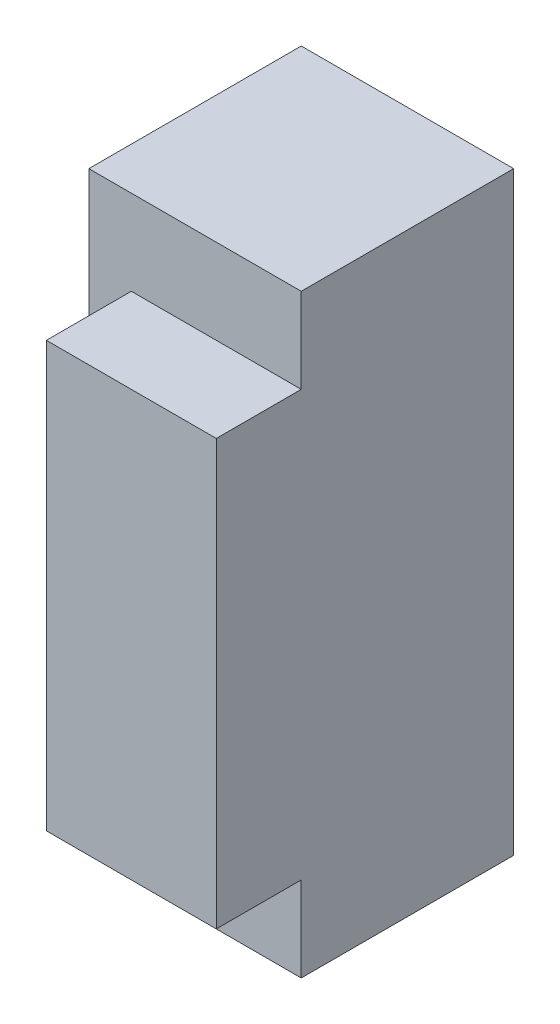
SolidWorks part; units mm, degrees
ref_plane "Front Plane" through (0, 0, 0) normal (0, 0, 1) x (1, 0, 0)
ref_plane "Top Plane" through (0, 0, 0) normal (0, 1, 0) x (1, 0, 0)
ref_plane "Right Plane" through (0, 0, 0) normal (1, 0, 0) x (0, 0, -1)
sketch "Sketch1" plane through (0, 0, 0) normal (0, 0, 1) x (1, 0, 0)
  line L1 (-2.5, 7) -> (2.5, 7)
  line L2 (-2.5, 7) -> (-2.5, -7)
  line L3 (-2.5, -7) -> (2.5, -7)
  line L4 (2.5, 7) -> (2.5, -7)
  point P4 (2.5, 0)
  point P6 (0, 7)
  dimension "D1" = 14
  dimension "D2" = 5
extrude "Extrude1" add sketch "Sketch1" along normal blind 5
sketch "Sketch2" plane through (0, 0, 5) normal (0, 0, 1) x (1, 0, 0)
  line L0 (2.5, -7) -> (2.5, 7) construction
  line L1 (2.5, -5) -> (-1.5, -5)
  line L2 (2.5, -5) -> (2.5, 5)
  line L3 (2.5, 5) -> (-1.5, 5)
  line L4 (-1.5, -5) -> (-1.5, 5)
  point P6 (2.5, 0)
  point P7 (2.5, 0)
  dimension "D1" = 4
  dimension "D2" = 10
extrude "Extrude2" add sketch "Sketch2" along normal blind 2
